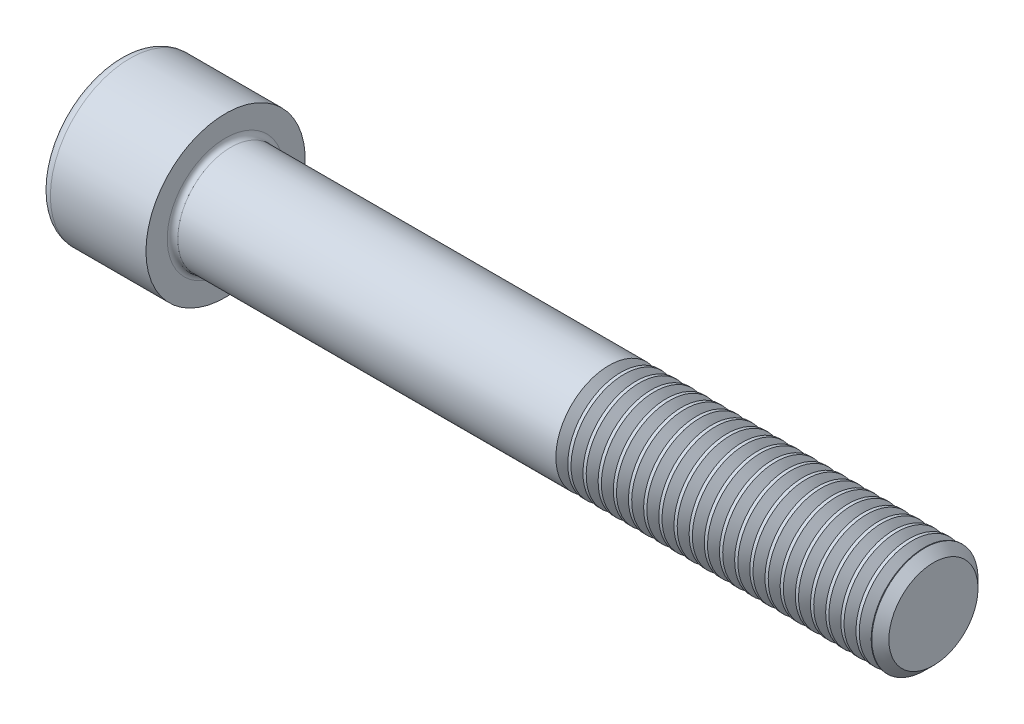
SolidWorks part; units mm, degrees
revolve "Base-Revolve" add sketch "BodySke"
sketch "BodySke" plane through (0, 0, 0) normal (0, 0, 1) x (1, 0, 0)
  line L0 (0, 0) -> (0, 9)
  line L1 (0, 9) -> (12, 9)
  line L2 (12, 9) -> (12, 6)
  line L3 (12, 6) -> (91.036, 6)
  line L4 (92, 5.036) -> (92, 0)
  line L5 (92, 0) -> (0, 0)
  line L6 (-31.75, 0) -> (127, 0) construction
  line L8 (92, 5.036) -> (91.036, 6)
  line L10 (92, -5.036) -> (91.036, -6) construction
  line L11 (13.75, 9.525) -> (13.75, 3.175) construction
  line L12 (56, 9.525) -> (56, 3.175) construction
  line L13 (32, 9.525) -> (32, 3.175) construction
cosmetic thread "ThreadCosmetic" [suppressed]
fillet "Fillet1" radius 0.6 1 edges at (12, 0, 6)
fillet "Fillet2" radius 1.2 1 edges at (0, 0, 9)
ref_plane "Plane1" through (0, 0, 0) normal (0, 0, 1) x (1, 0, 0)
ref_plane "Plane2" through (0, 0, 0) normal (0, 1, 0) x (1, 0, 0)
ref_plane "Plane3" through (0, 0, 0) normal (1, 0, 0) x (0, 0, -1)
sketch "Sketch2" plane through (0, 0, 0) normal (0, 0, 1) x (1, 0, 0)
  line L0 (0, 5.0125) -> (6, 5.0125)
  line L1 (6, 5.0125) -> (8.894, 0)
  line L2 (-31.75, 0) -> (127, 0) construction
  line L3 (8.894, 0) -> (0, 0)
  line L4 (0, 0) -> (0, 5.0125)
  line L6 (0, 0) -> (47.625, 0) construction
revolve "Hex-PreBroach" cut sketch "Sketch2" angle 360 about L6
sketch "Sketch3" plane through (0, 0, 0) normal (-1, 0, 0) x (0, 0.5, 0.866)
  line L0 (2.894, 5.0125) -> (-2.894, 5.0125)
  line L1 (-2.894, 5.0125) -> (-5.7879, 0)
  line L2 (2.894, 5.0125) -> (5.7879, 0)
  line L3 (2.894, -5.0125) -> (5.7879, 0)
  line L4 (2.894, -5.0125) -> (-2.894, -5.0125)
  line L5 (-2.894, -5.0125) -> (-5.7879, 0)
extrude "Hex" cut sketch "Sketch3" against normal blind 6
sketch "ThdSchSke" plane through (0, 0, 0) normal (0, 0, 1) x (1, 0, 0)
  line L0 (56, -5.036) -> (55.325, -6)
  line L1 (56, -5.036) -> (56.675, -6)
  line L2 (56.675, -6) -> (56.675, -7.5)
  line L3 (-3.175, 0) -> (5.1513, 0) construction
  line L4 (0, 7.8) -> (0, -7.8) construction
  line L5 (56.675, -7.5) -> (55.325, -7.5)
  line L6 (55.325, -7.5) -> (55.325, -6)
revolve "ThreadSchematic" cut sketch "ThdSchSke" angle 360 about L3
pattern_linear "ThdSchPat" count 21 spacing 1.7143 along (1, 0, 0) of "ThreadSchematic"
equation "\"D2@Sketch3\" = \"Hex_size@Sketch3\" / 2"
equation "\"D1@Sketch3\" = \"Hex_size@Sketch3\" / 2"
equation "\"D1@Sketch2\" = \"Hex_size@Sketch3\" / 2"
equation "\"Thread_minor@ThreadCosmetic\"  =  \"Minor_dia@BodySke\""
equation "\"Depth@Sketch2\" =  \"Key_eng@Hex\""
equation "\"Thread_length@ThreadCosmetic\" = ((sgn( (\"Length@BodySke\" - \"Advance@BodySke\" * 3.0) - \"Thread_nom@BodySke\" )-1)*( (\"Length@BodySke\" - \"Advance@BodySke\" * 3.0) - \"Thread_nom@BodySke\" ))/-2+ \"Thread_nom@BodySke\""
equation "\"Thread_minor@ThdSchSke\" = \"Minor_dia@BodySke\""
equation "\"Diameter@ThdSchSke\" = \"Diameter@BodySke\""
equation "\"Overcut@ThdSchSke\" = \"Diameter@BodySke\" * 1.25"
equation "\"Start@ThdSchSke\" = \"Head_ht@BodySke\" + \"Length@BodySke\" - \"Thread_length@ThreadCosmetic\"  '---Non-countersunk---"
equation "\"Num_threads@ThdSchPat\" = int( \"Thread_length@ThreadCosmetic\" / \"Advance@BodySke\" + 0.999 )  + 1"
equation "\"Advance@ThdSchPat\" = \"Thread_length@ThreadCosmetic\" /  (\"Num_threads@ThdSchPat\" - 1) 'relax it"
equation "\"Num_threads@ThdSchPat\" = \"Num_threads@ThdSchPat\" - sgn( \"Num_threads@ThdSchPat\" - 1) '---chamfered tips only---"
